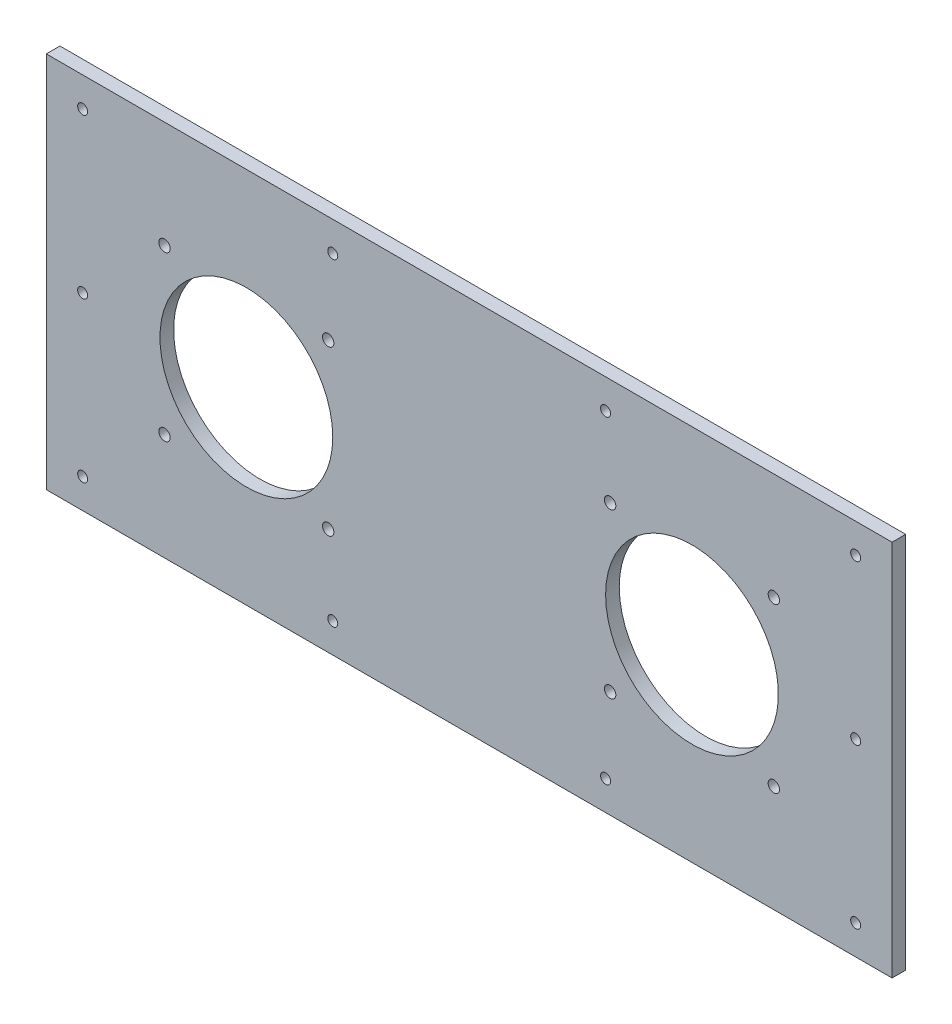
SolidWorks part; units mm, degrees
ref_plane "Plan de face" through (0, 0, 0) normal (0, 0, 1) x (1, 0, 0)
ref_plane "Plan de dessus" through (0, 0, 0) normal (0, 1, 0) x (1, 0, 0)
ref_plane "Plan de droite" through (0, 0, 0) normal (1, 0, 0) x (0, 0, -1)
sketch "Esquisse1" plane through (0, 0, 0) normal (0, 0, 1) x (1, 0, 0)
  line L0 (-186, 0) -> (0, 0) construction
  line L1 (186, 83) -> (-186, 83)
  line L2 (186, 83) -> (186, -83)
  line L3 (186, -83) -> (-186, -83)
  line L4 (-186, 83) -> (-186, -83)
  line L5 (186, 83) -> (-186, -83) construction
  line L6 (186, -83) -> (-186, 83) construction
  line L7 (0, 0) -> (0, 83) construction
  line L8 (-186, 70) -> (186, 70) construction
  line L9 (-186, -70) -> (186, -70) construction
  line L10 (-170, 70) -> (-170, -70) construction
  line L11 (170, 70) -> (170, -70) construction
  circle A0 centre (-170, 70) radius 2.2
  circle A1 centre (-60, 70) radius 2.2
  circle A2 centre (60, 70) radius 2.2
  circle A3 centre (170, 70) radius 2.2
  circle A4 centre (170, -70) radius 2.2
  circle A5 centre (60, -70) radius 2.2
  circle A6 centre (-60, -70) radius 2.2
  circle A7 centre (-170, -70) radius 2.2
  circle A8 centre (-170, 0) radius 2.2
  circle A9 centre (170, 0) radius 2.2
  point P0 (0, 0)
  dimension "D4" = 4.4
  dimension "D1" = 166
  dimension "D2" = 372
  dimension "D3" = 13
  dimension "D5" = 16
  dimension "D6" = 60
  dimension "D7" = 140
  dimension "D8" = 340
extrude "Boss.-Extru.1" add sketch "Esquisse1" along normal blind 6
sketch "Esquisse2" plane through (0, 0, 6) normal (0, 0, 1) x (1, 0, 0)
  line L0 (-186, 0) -> (0, 0) construction
  line L1 (-186, 83) -> (-186, -83) construction
  line L2 (0, 0) -> (0, 83) construction
  line L3 (186, 83) -> (-186, 83) construction
  line L4 (-98, 0) -> (-98, 38) construction
  line L5 (98, 0) -> (98, 38) construction
  circle A0 centre (-98, 0) radius 38
  circle A1 centre (-134, 36) radius 2.5
  circle A2 centre (-134, -36) radius 2.5
  circle A3 centre (-62, -36) radius 2.5
  circle A4 centre (-62, 36) radius 2.5
  circle A5 centre (62, 36) radius 2.5
  circle A6 centre (62, -36) radius 2.5
  circle A7 centre (134, -36) radius 2.5
  circle A8 centre (134, 36) radius 2.5
  circle A9 centre (98, 0) radius 38
  dimension "D1" = 76
  dimension "D3" = 5
  dimension "D2" = 72
  dimension "D4" = 72
  dimension "D5" = 88
extrude "Enlèv. mat.-Extru.1" cut sketch "Esquisse2" against normal through all
